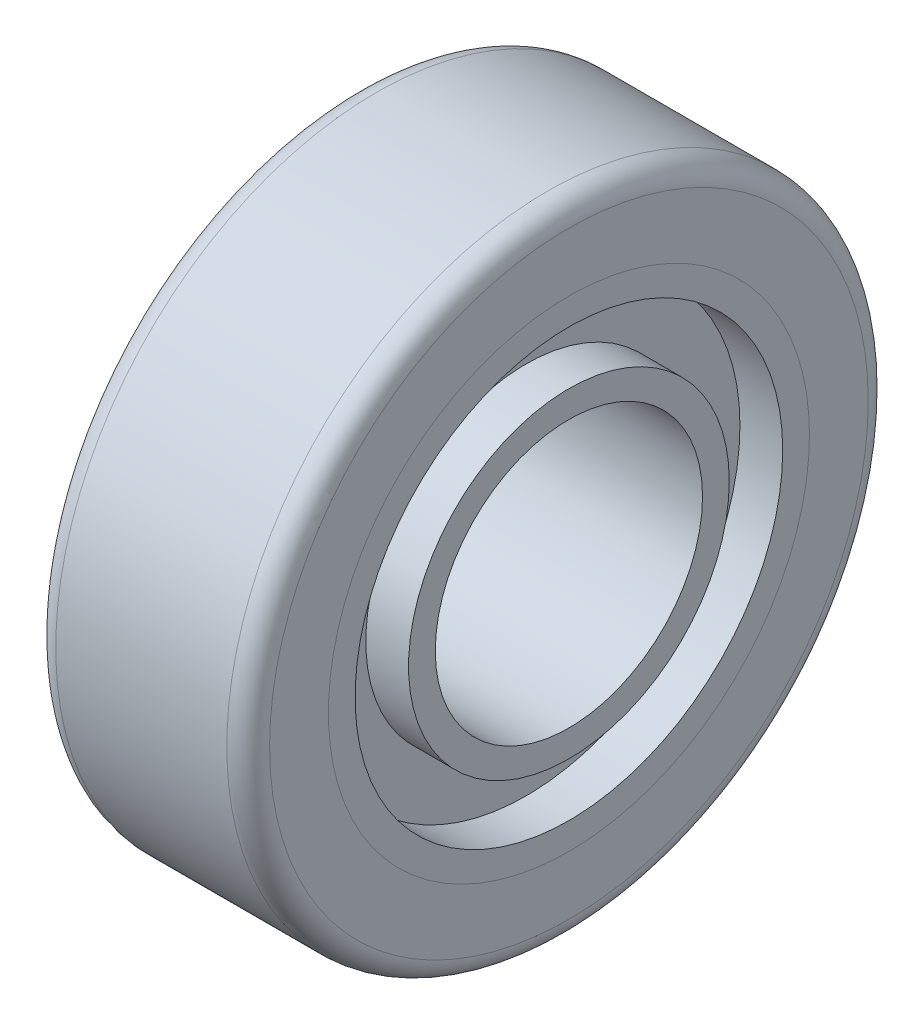
SolidWorks part; units mm, degrees
ref_plane "Front Plane" through (0, 0, 0) normal (0, 0, 1) x (1, 0, 0)
ref_plane "Top Plane" through (0, 0, 0) normal (0, 1, 0) x (1, 0, 0)
ref_plane "Right Plane" through (0, 0, 0) normal (1, 0, 0) x (0, 0, -1)
sketch "Sketch1" plane through (0, 0, 0) normal (1, 0, 0) x (0, 0, -1)
  circle A0 centre (0, 0) radius 38.1
  dimension "D1" = 76.2
extrude "Boss-Extrude1" add sketch "Sketch1" along normal blind 25.4
fillet "Fillet2" radius 2.54 2 edges at (0, 0, -38.1) (25.4, 0, -38.1)
sketch "Sketch2" plane through (25.4, 0, 0) normal (1, 0, 0) x (0, 0, -1)
  circle A0 centre (0, 0) radius 28.575
  dimension "D1" = 57.15
extrude "Cut-Extrude1" cut sketch "Sketch2" against normal blind 25.4
sketch "Sketch3" plane through (25.4, 0, 0) normal (1, 0, 0) x (0, 0, -1)
  circle A0 centre (0, 0) radius 28.575
extrude "Boss-Extrude3" add sketch "Sketch3" against normal blind 25.4 separate body
sketch "Sketch7" plane through (25.4, 0, 0) normal (1, 0, 0) x (0, 0, -1)
  circle A0 centre (0, 0) radius 19.05
  circle A1 centre (0, 0) radius 25.4
  dimension "D1" = 38.1
  dimension "D2" = 50.8
extrude "Cut-Extrude3" cut sketch "Sketch7" against normal blind 5.08
sketch "Sketch8" plane through (25.4, 0, 0) normal (1, 0, 0) x (0, 0, -1)
  circle A0 centre (0, 0) radius 15.875
  dimension "D1" = 31.75
extrude "Cut-Extrude4" cut sketch "Sketch8" against normal blind 25.4
ref_plane "Plane2" through (12.7, 0, 0) normal (-1, 0, 0) x (0, 0, 1)
mirror "Mirror1" about plane through (12.7, 0, 0) normal (-1, 0, 0) of "Cut-Extrude3"
